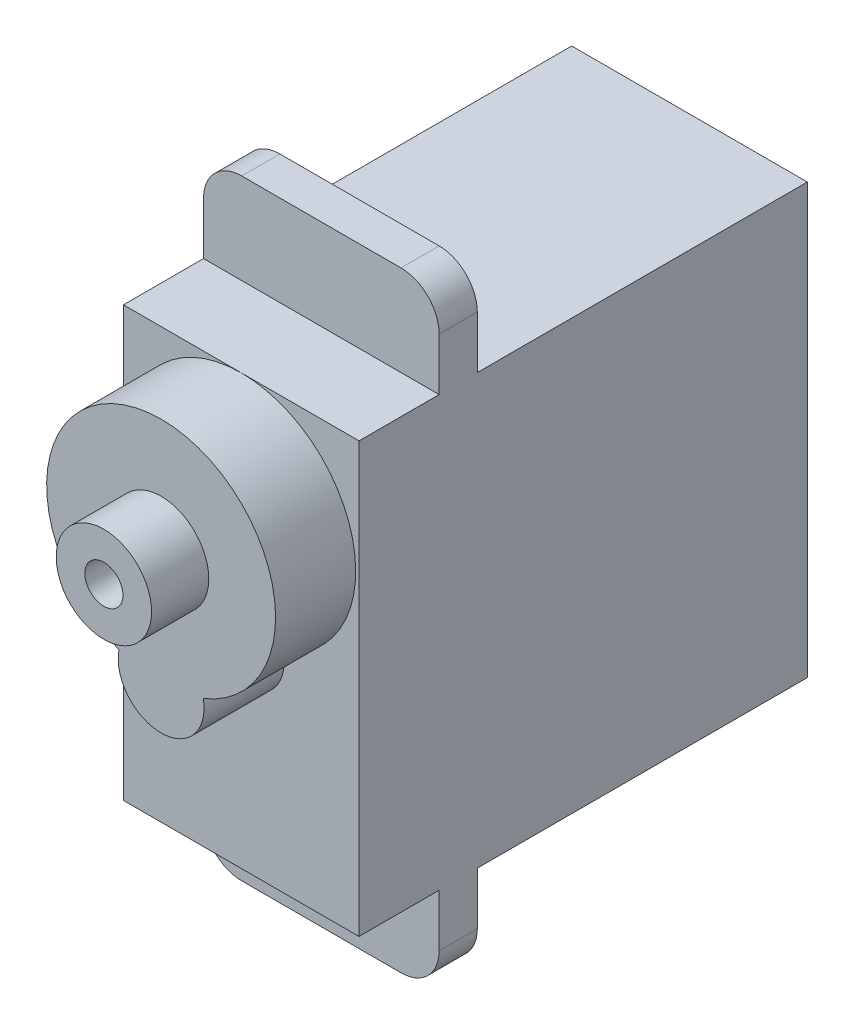
SolidWorks part; units mm, degrees
ref_plane "Front Plane" through (0, 0, 0) normal (0, 0, 1) x (1, 0, 0)
ref_plane "Top Plane" through (0, 0, 0) normal (0, 1, 0) x (1, 0, 0)
ref_plane "Right Plane" through (0, 0, 0) normal (1, 0, 0) x (0, 0, -1)
sketch "Sketch3" plane through (0, -28.2755, 0) normal (1, 0, 0) x (0, 1, 0)
  line L1 (35.8597, 178.8667) -> (13.3597, 178.8667)
  line L2 (35.8597, 178.8667) -> (35.8597, 155.3667)
  line L3 (35.8597, 155.3667) -> (13.3597, 155.3667)
  line L4 (13.3597, 178.8667) -> (13.3597, 155.3667)
  dimension "D1" = 22.5
  dimension "D2" = 23.5
extrude "Boss-Extrude1" add sketch "Sketch3" along normal mid plane 12.35
ref_plane "Plane1" through (0, 0, 174.6667) normal (0, 0, 1) x (1, 0, 0)
sketch "Sketch4" plane through (0, 0, 174.6667) normal (0, 0, 1) x (1, 0, 0)
  line L0 (-6.175, 7.5842) -> (-6.175, -14.9158) construction
  line L1 (-6.175, 12.3342) -> (6.175, 12.3342)
  line L2 (-6.175, 12.3342) -> (-6.175, -19.6658)
  line L3 (-6.175, -19.6658) -> (6.175, -19.6658)
  line L4 (6.175, 12.3342) -> (6.175, -19.6658)
  line L5 (6.175, 7.5842) -> (6.175, -14.9158) construction
  line L6 (0, 7.5842) -> (0, -14.9158) construction
  line L7 (6.175, 7.5842) -> (-6.175, 7.5842) construction
  line L8 (6.175, -14.9158) -> (-6.175, -14.9158) construction
  line L9 (0, -3.6658) -> (2.6217, -3.6658) construction
  dimension "D1" = 0
  dimension "D2" = 0
  dimension "D3" = 32
  dimension "D4" = 16
extrude "Boss-Extrude2" add sketch "Sketch4" against normal blind 2
sketch "Sketch5" plane through (0, 0, 178.8667) normal (0, 0, 1) x (1, 0, 0)
  line L0 (6.175, 7.5842) -> (-6.175, 7.5842) construction
  arc A0 (2.2101, -3.9939) -> (-2.2101, -3.9939) centre (0, 1.5842) ccw
  arc A1 (-2.2101, -3.9939) -> (2.2101, -3.9939) centre (0, -4.4158) ccw
  dimension "D1" = 12
  dimension "D2" = 6
  dimension "D3" = 4.5
extrude "Boss-Extrude3" add sketch "Sketch5" along normal blind 4.2
sketch "Sketch6" plane through (0, 0, 183.0667) normal (0, 0, 1) x (1, 0, 0)
  circle A0 centre (0, 1.5842) radius 2.5
  dimension "D1" = 5
extrude "Cut-Extrude1" cut sketch "Sketch6" against normal blind 4.2
fillet "Fillet1" radius 2 4 edges at (6.175, -19.6658, 173.6667) (-6.175, -19.6658, 173.6667) (6.175, 12.3342, 173.6667) (-6.175, 12.3342, 173.6667)
sketch "Sketch7" plane through (0, 0, 178.8667) normal (0, 0, 1) x (1, 0, 0)
  circle A0 centre (0, 1.5842) radius 2.5
extrude "Boss-Extrude4" add sketch "Sketch7" along normal blind 7.2
sketch "Sketch8" plane through (0, 0, 186.0667) normal (0, 0, 1) x (1, 0, 0)
  circle A0 centre (0, 1.5842) radius 1
extrude "Cut-Extrude2" cut sketch "Sketch8" against normal blind 7
